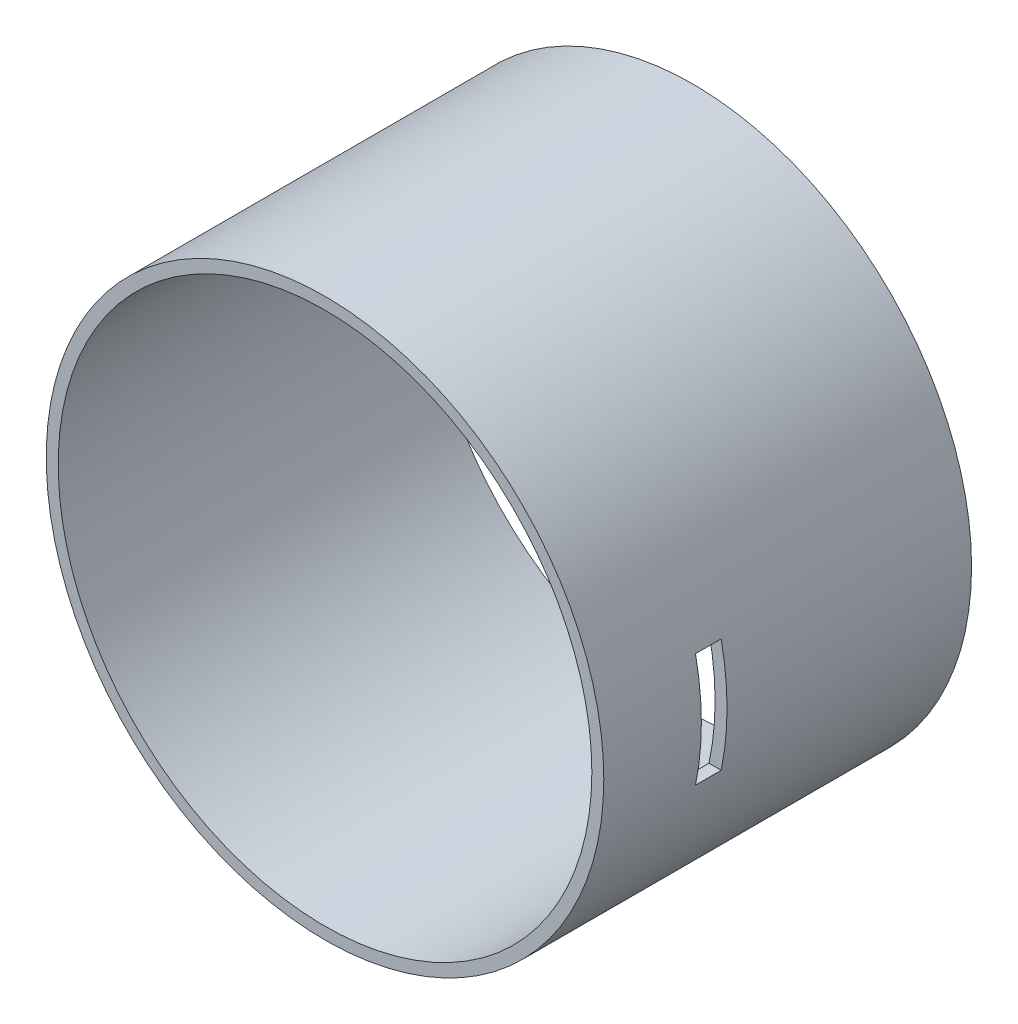
SolidWorks part; units mm, degrees
material "6061-T6 (SS)"
ref_plane "Front" through (0, 0, 0) normal (0, 0, 1) x (1, 0, 0)
ref_plane "Top" through (0, 0, 0) normal (0, 1, 0) x (1, 0, 0)
ref_plane "Right" through (0, 0, 0) normal (1, 0, 0) x (0, 0, -1)
sketch "Sketch1" plane through (0, 0, 0) normal (0, 0, 1) x (1, 0, 0)
  circle A0 centre (0, 0) radius 140
  circle A1 centre (0, 0) radius 134
extrude "Boss-Extrude1" add sketch "Sketch1" along normal blind 184.7 contours A1 | A0
hole_wizard "M2x0.4 Tapped Hole2" positions "Sketch3" profile "Sketch4" tap size "M2x0.4" standard "ANSI Metric"
sketch "Sketch3" plane through (0, 0, 0) normal (0, 0, -1) x (-1, 0, 0)
  point P0 (0, 137)
  point P1 (137, 0)
  point P3 (93.9554, 99.1162)
  point P5 (96.874, -96.874)
  point P9 (0, -137)
  point P11 (-96.874, -96.874)
  point P13 (-137, 0)
  point P15 (-96.874, 96.874)
cosmetic thread "Hole Thread10" parameters "D1"=2.4, "D2"=2
cosmetic thread "Hole Thread11" parameters "D1"=2.4, "D2"=2
cosmetic thread "Hole Thread12" parameters "D1"=2.4, "D2"=2
cosmetic thread "Hole Thread13" parameters "D1"=2.4, "D2"=2
cosmetic thread "Hole Thread14" parameters "D1"=2.4, "D2"=2
cosmetic thread "Hole Thread15" parameters "D1"=2.4, "D2"=2
cosmetic thread "Hole Thread16" parameters "D1"=2.4, "D2"=2
cosmetic thread "Hole Thread17" parameters "D1"=2.4, "D2"=2
sketch "Sketch4" plane through (0, 137, 0) normal (1, 0, 0) x (0, 1, 0)
  line L0 (0, 0) -> (0, 4.0807)
  line L1 (0, 4.0807) -> (0.8, 3.6)
  line L2 (0.8, 3.6) -> (0.8, 0)
  line L5 (0.8, 0) -> (0, 0)
  line L10 (0, 4.0807) -> (-0.8, 3.6) construction
  line L11 (0, -6.35) -> (0, 107.95) construction
  dimension "Tap Drill Dia." = 1.6
  dimension "Tap Drill Depth" = 3.6
  dimension "Drill Angle" = 118
sketch "Sketch5" plane through (0, 0, 0) normal (1, 0, 0) x (0, 0, -1)
  line L1 (-122.8, 28.575) -> (-135.7, 28.575)
  line L2 (-122.8, 28.575) -> (-122.8, -28.575)
  line L3 (-122.8, -28.575) -> (-135.7, -28.575)
  line L4 (-135.7, 28.575) -> (-135.7, -28.575)
extrude "Cut-Extrude1" cut sketch "Sketch5" along normal blind 140
